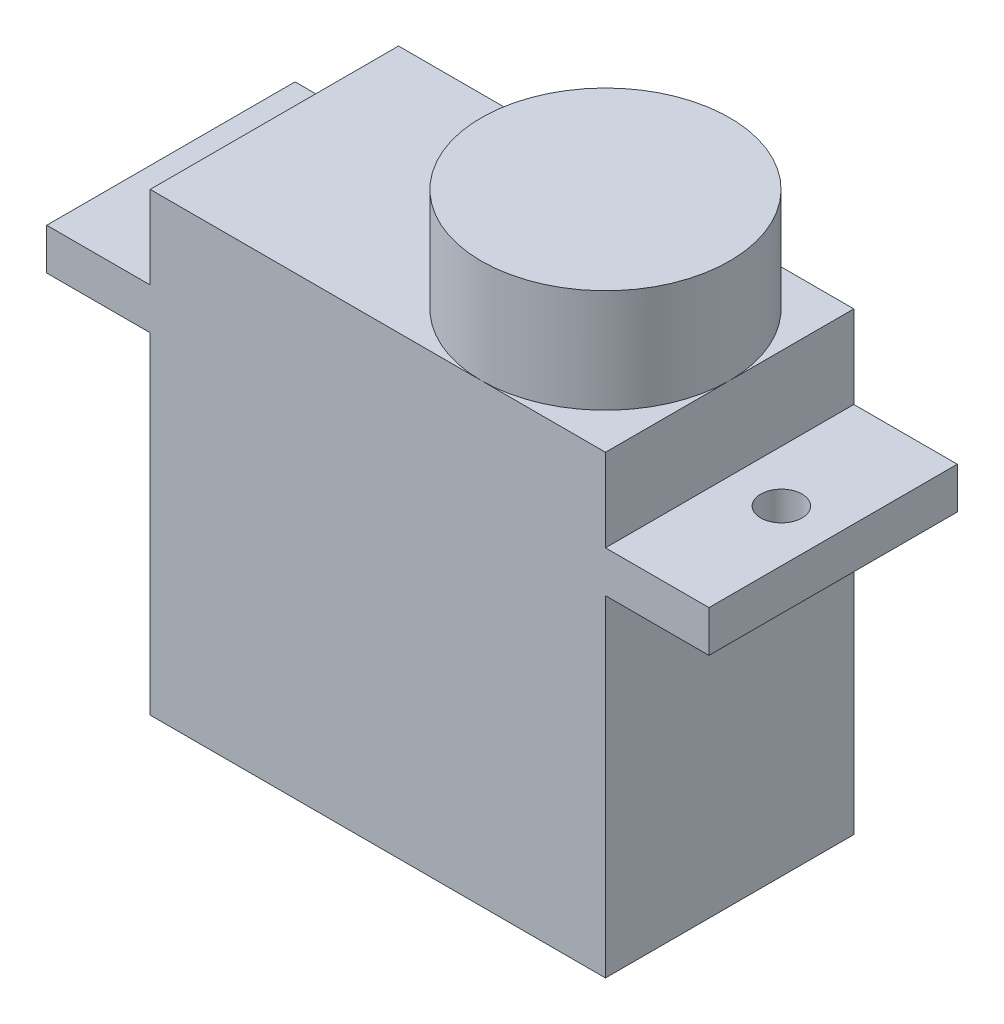
SolidWorks part; units mm, degrees
ref_plane "Front Plane" through (0, 0, 0) normal (0, 0, 1) x (1, 0, 0)
ref_plane "Top Plane" through (0, 0, 0) normal (0, 1, 0) x (1, 0, 0)
ref_plane "Right Plane" through (0, 0, 0) normal (1, 0, 0) x (0, 0, -1)
sketch "Sketch1" plane through (0, 0, 0) normal (0, 1, 0) x (1, 0, 0)
  line L1 (0, 0) -> (22, 0)
  line L2 (0, 0) -> (0, 12)
  line L3 (0, 12) -> (22, 12)
  line L4 (22, 0) -> (22, 12)
  dimension "D1" = 22
  dimension "D2" = 12
extrude "Boss-Extrude1" add sketch "Sketch1" along normal blind 22
sketch "Sketch2" plane through (0, 0, 0) normal (0, 0, 1) x (1, 0, 0)
  line L0 (0, 0) -> (22, 0) construction
  line L1 (-5, 18) -> (27, 18)
  line L2 (-5, 18) -> (-5, 16)
  line L3 (-5, 16) -> (27, 16)
  line L4 (27, 18) -> (27, 16)
  dimension "D1" = 32
  dimension "D2" = 2
  dimension "D3" = 5
  dimension "D4" = 16
extrude "Boss-Extrude2" add sketch "Sketch2" against normal through all
sketch "Sketch3" plane through (0, 18, 0) normal (0, 1, 0) x (1, 0, 0)
  line L0 (-5, 12) -> (-5, 0) construction
  line L1 (0, 0) -> (-5, 0) construction
  line L2 (27, 12) -> (27, 0) construction
  line L3 (27, 0) -> (22, 0) construction
  circle A0 centre (-2.5, 6) radius 1
  circle A1 centre (24.5, 6) radius 1
  point P4 (-5, 6)
  point P9 (27, 6)
  point P12 (24.5, 0)
  dimension "D1" = 2
  dimension "D2" = 2
  dimension "D3" = 2.5
  dimension "D4" = 6
  dimension "D5" = 2.5
  dimension "D6" = 6
extrude "Cut-Extrude1" cut sketch "Sketch3" against normal blind 22
sketch "Sketch5" plane through (0, 22, 0) normal (0, 1, 0) x (1, 0, 0)
  line L0 (22, 6) -> (16, 6) construction
  line L1 (22, 0) -> (22, 12) construction
  circle A0 centre (16, 6) radius 6
  dimension "D1" = 6
extrude "Boss-Extrude3" add sketch "Sketch5" along normal blind 5
